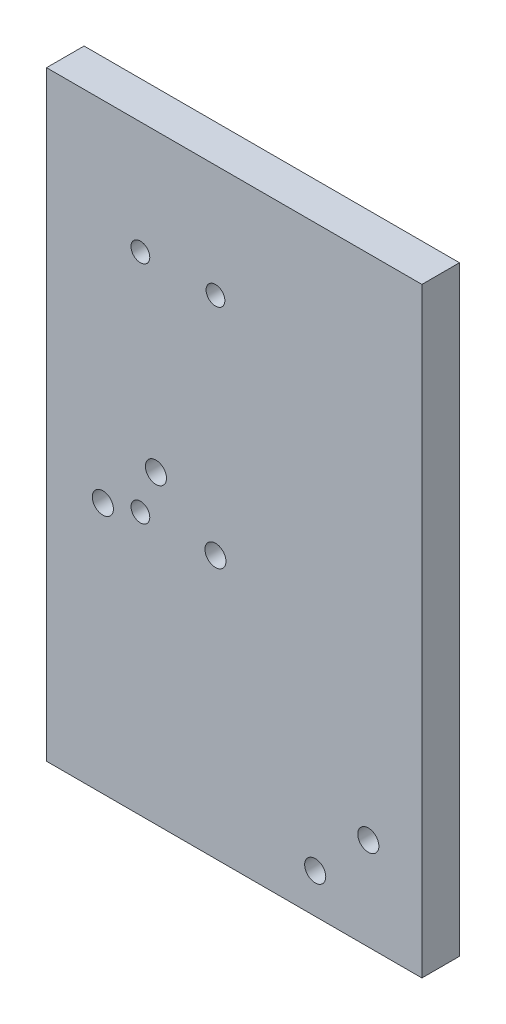
SolidWorks part; units mm, degrees
material "6061-T6 (SS)"
ref_plane "Front" through (0, 0, 0) normal (0, 0, 1) x (1, 0, 0)
ref_plane "Top" through (0, 0, 0) normal (0, 1, 0) x (1, 0, 0)
ref_plane "Right" through (0, 0, 0) normal (1, 0, 0) x (0, 0, -1)
sketch "Sketch1" plane through (0, 0, 0) normal (0, 0, 1) x (1, 0, 0)
  line L1 (54.4059, 466.3778) -> (181.397, 466.3778)
  line L4 (54.4059, 466.3778) -> (54.4059, 263.1761)
  line L5 (54.4059, 263.1761) -> (181.397, 263.1761)
  line L6 (181.397, 263.1761) -> (181.397, 466.3778)
  circle A0 centre (73.4559, 348.3897) radius 5.5499 construction
  circle A1 centre (163.2585, 294.5081) radius 3.5687
  circle A2 centre (91.4164, 366.3502) radius 5.5499 construction
  circle A3 centre (145.298, 276.5476) radius 3.5687
  circle A4 centre (145.298, 276.5476) radius 5.5499 construction
  circle A5 centre (91.4164, 366.3502) radius 3.5687
  circle A6 centre (163.2585, 294.5081) radius 5.5499 construction
  circle A7 centre (73.4559, 348.3897) radius 3.5687
  circle A13 centre (86.1559, 428.2778) radius 3.175
  circle A15 centre (111.5559, 428.2778) radius 3.175
  circle A17 centre (86.1559, 352.0778) radius 3.175
  circle A19 centre (111.5559, 352.0778) radius 3.556
  point P1 (187.4422, 245.1167)
  point P4 (187.4422, 466.3778)
  point P9 (54.4059, 257.8167)
  point P10 (200.1422, 257.8167)
  dimension "D1" = 76.2
  dimension "D2" = 25.4
  dimension "D3" = 25.4
  dimension "D4" = 101.6
  dimension "D5" = 25.4
  dimension "D6" = 101.6
  dimension "D7" = 19.05
  dimension "D8" = 31.75
  dimension "D9" = 38.1
  dimension "D10" = 203.2017
  dimension "D12" = 85.2135
  dimension "D13" = 6.35
  dimension "D14" = 6.35
  dimension "D15" = 6.35
  dimension "D16" = 7.1374
  dimension "D17" = 7.1374
  dimension "D18" = 7.1374
  dimension "D19" = 7.1374
  dimension "D20" = 11.0998
  dimension "D21" = 11.0998
  dimension "D11" = 126.991
extrude "Boss-Extrude1" add sketch "Sketch1" along normal blind 12.7
sketch "Sketch2" plane through (0, 0, 0) normal (0, 0, -1) x (-1, 0, 0)
  circle A0 centre (-91.4164, 366.3502) radius 5.5499
  circle A1 centre (-73.4559, 348.3897) radius 5.5499
  circle A2 centre (-163.2585, 294.5081) radius 5.5499
  circle A3 centre (-145.298, 276.5476) radius 5.5499
  dimension "D1" = 11.0998
  dimension "D2" = 11.0998
  dimension "D3" = 11.0998
  dimension "D4" = 11.0998
extrude "Cut-Extrude1" cut sketch "Sketch2" against normal blind 7.1374
